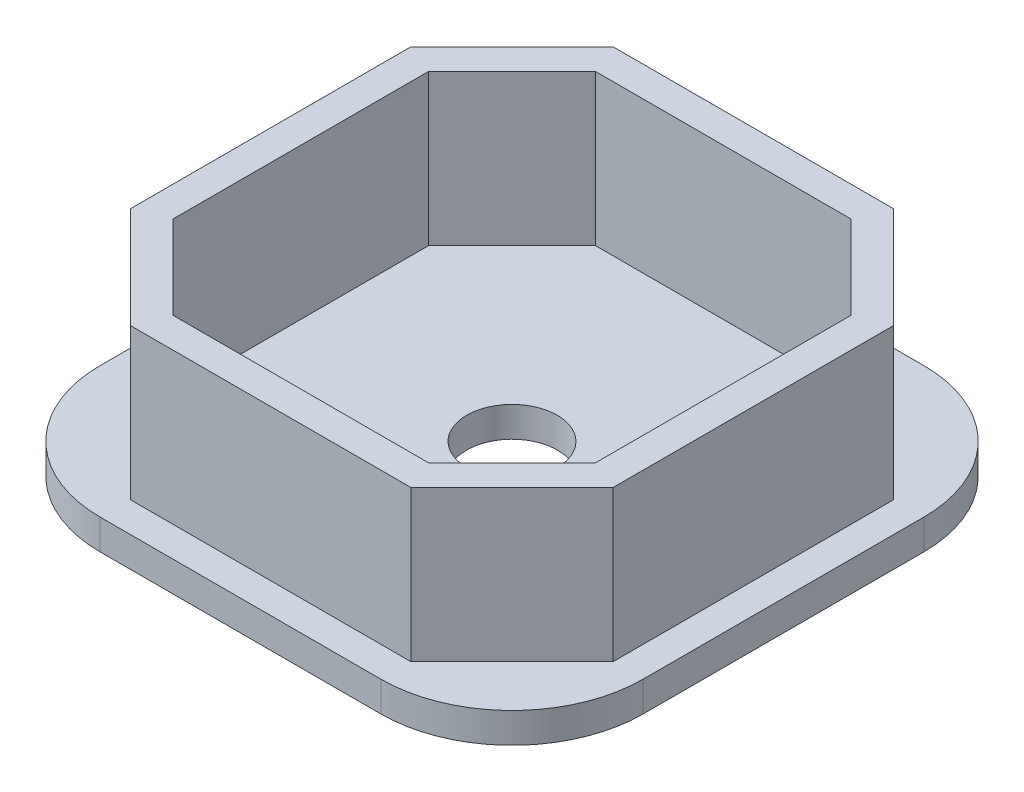
SolidWorks part; units mm, degrees
ref_plane "Front Plane" through (0, 0, 0) normal (0, 0, 1) x (1, 0, 0)
ref_plane "Top Plane" through (0, 0, 0) normal (0, 1, 0) x (1, 0, 0)
ref_plane "Right Plane" through (0, 0, 0) normal (1, 0, 0) x (0, 0, -1)
sketch "Sketch1" plane through (0, 0, 0) normal (0, 1, 0) x (1, 0, 0)
  line L1 (-4.65, -9) -> (4.65, -9)
  line L2 (-9, -4.65) -> (-9, 4.65)
  line L3 (-4.65, 9) -> (4.65, 9)
  line L4 (9, -4.65) -> (9, 4.65)
  line L5 (-9, -9) -> (9, 9) construction
  line L6 (-9, 9) -> (9, -9) construction
  arc A0 (-4.65, -9) -> (-9, -4.65) centre (-4.65, -4.65) cw
  arc A1 (9, -4.65) -> (4.65, -9) centre (4.65, -4.65) cw
  arc A2 (4.65, 9) -> (9, 4.65) centre (4.65, 4.65) cw
  arc A3 (-9, 4.65) -> (-4.65, 9) centre (-4.65, 4.65) cw
  circle A4 centre (0, 0) radius 1.5
  point P0 (0, 0)
  dimension "D3" = 4.35
  dimension "D4" = 3
  dimension "D1" = 18
  dimension "D2" = 18
extrude "Boss-Extrude1" add sketch "Sketch1" along normal blind 1
sketch "Sketch2" plane through (0, 1, 0) normal (0, 1, 0) x (1, 0, 0)
  line L0 (-8, 4.65) -> (-4.65, 8)
  line L1 (-4.65, -8) -> (4.65, -8)
  line L2 (-8, -4.65) -> (-8, 4.65)
  line L3 (-4.65, 8) -> (4.65, 8)
  line L4 (8, -4.65) -> (8, 4.65)
  line L5 (-8, -8) -> (8, 8) construction
  line L6 (-8, 8) -> (8, -8) construction
  line L7 (4.65, 8) -> (8, 4.65)
  line L8 (-4.65, -8) -> (-8, -4.65)
  line L9 (4.65, -8) -> (8, -4.65)
  line L10 (-7, 4.2358) -> (-4.2358, 7)
  line L11 (-4.2358, 7) -> (4.2358, 7)
  line L12 (4.2358, 7) -> (7, 4.2358)
  line L13 (7, -4.2358) -> (7, 4.2358)
  line L14 (4.2358, -7) -> (7, -4.2358)
  line L15 (-4.2358, -7) -> (4.2358, -7)
  line L16 (-4.2358, -7) -> (-7, -4.2358)
  line L17 (-7, -4.2358) -> (-7, 4.2358)
  point P0 (0, 0)
  dimension "D3" = 1
  dimension "D1" = 16
  dimension "D2" = 16
extrude "Boss-Extrude2" add sketch "Sketch2" along normal blind 5
